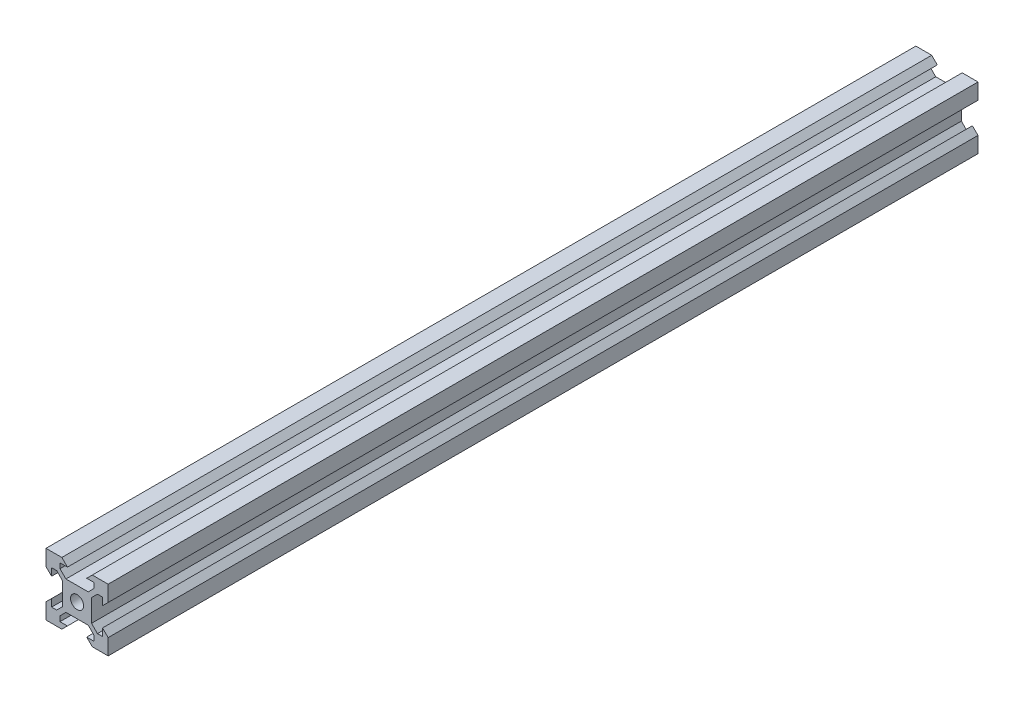
SolidWorks part; units mm, degrees
material "6063-T5"
ref_plane "Front Plane" through (0, 0, 0) normal (0, 0, 1) x (1, 0, 0)
ref_plane "Top Plane" through (0, 0, 0) normal (0, 1, 0) x (1, 0, 0)
ref_plane "Right Plane" through (0, 0, 0) normal (1, 0, 0) x (0, 0, -1)
sketch "Sketch1" plane through (0, 0, 0) normal (0, 0, 1) x (1, 0, 0)
  line L0 (3.59, 4.6507) -> (-3.59, 4.6507)
  line L5 (-10, -10) -> (10, -10)
  line L6 (-10, -10) -> (-10, 10)
  line L7 (-10, 10) -> (10, 10)
  line L8 (10, -10) -> (10, 10)
  line L9 (-10, -10) -> (10, 10) construction
  line L10 (-10, 10) -> (10, -10) construction
  line L11 (0, 10) -> (0, -10) construction
  line L12 (10, 0) -> (-10, 0) construction
  line L13 (-3.59, 4.6507) -> (-5.4993, 6.56)
  line L14 (-5.4993, 6.56) -> (-5.4993, 8.2)
  line L15 (3.59, 4.6507) -> (5.4993, 6.56)
  line L16 (5.4993, 6.56) -> (5.4993, 8.2)
  line L17 (5.4993, 8.2) -> (3.1, 8.2)
  line L18 (3.1, 8.2) -> (4.9, 10)
  line L19 (-5.4993, 8.2) -> (-3.1, 8.2)
  line L20 (-3.1, 8.2) -> (-4.9, 10)
  line L21 (3.1, -8.2) -> (4.9, -10)
  line L22 (5.4993, -8.2) -> (3.1, -8.2)
  line L23 (5.4993, -6.56) -> (5.4993, -8.2)
  line L24 (3.59, -4.6507) -> (5.4993, -6.56)
  line L25 (3.59, -4.6507) -> (-3.59, -4.6507)
  line L26 (-3.59, -4.6507) -> (-5.4993, -6.56)
  line L27 (-5.4993, -6.56) -> (-5.4993, -8.2)
  line L28 (-5.4993, -8.2) -> (-3.1, -8.2)
  line L29 (-3.1, -8.2) -> (-4.9, -10)
  line L30 (8.2, 3.1) -> (10, 4.9)
  line L31 (8.2, 3.1) -> (8.2, 5.4993)
  line L32 (8.2, 5.4993) -> (6.56, 5.4993)
  line L33 (4.6507, 3.59) -> (6.56, 5.4993)
  line L34 (4.6507, 3.59) -> (4.6507, -3.59)
  line L35 (4.6507, -3.59) -> (6.56, -5.4993)
  line L36 (8.2, -5.4993) -> (6.56, -5.4993)
  line L37 (8.2, -3.1) -> (8.2, -5.4993)
  line L38 (8.2, -3.1) -> (10, -4.9)
  line L39 (-8.2, -3.1) -> (-10, -4.9)
  line L40 (-8.2, -3.1) -> (-8.2, -5.4993)
  line L41 (-8.2, -5.4993) -> (-6.56, -5.4993)
  line L42 (-4.6507, -3.59) -> (-6.56, -5.4993)
  line L43 (-4.6507, 3.59) -> (-4.6507, -3.59)
  line L44 (-4.6507, 3.59) -> (-6.56, 5.4993)
  line L45 (-8.2, 5.4993) -> (-6.56, 5.4993)
  line L46 (-8.2, 3.1) -> (-8.2, 5.4993)
  line L47 (-8.2, 3.1) -> (-10, 4.9)
  line L48 (4.9, 10) -> (-4.9, 10)
  line L49 (-10, 4.9) -> (-10, -4.9)
  line L50 (10, -4.9) -> (10, 4.9)
  line L51 (4.9, -10) -> (-4.9, -10)
  circle A1 centre (0, 0) radius 2.1
  point P11 (0, 4.6507)
  point P35 (4.6507, 0)
  dimension "D1" = 4.2
  dimension "D2" = 20
  dimension "D3" = 20
  dimension "D4" = 0.75
  dimension "D5" = 3.59
  dimension "D6" = 3.1
  dimension "D7" = 1.8
  dimension "D8" = 1.64
  dimension "D9" = 3.59
  dimension "D10" = 1.64
  dimension "D11" = 1.8
  dimension "D12" = 45
  dimension "D13" = 0.75
  dimension "D14" = 3.1
extrude "Boss-Extrude1" add sketch "Sketch1" along normal mid plane 280 contours L6 L5 L8 L7 | A1 | L50 L30 L31 L32 L33 L34 L35 L36 L37 L38 | L48 L20 L19 L14 L13 L0 L15 L16 L17 L18 | L49 L39 L40 L41 L42 L43 L44 L45 L46 L47 | L51 L29 L28 L27 L26 L25 L24 L23 L22 L21
